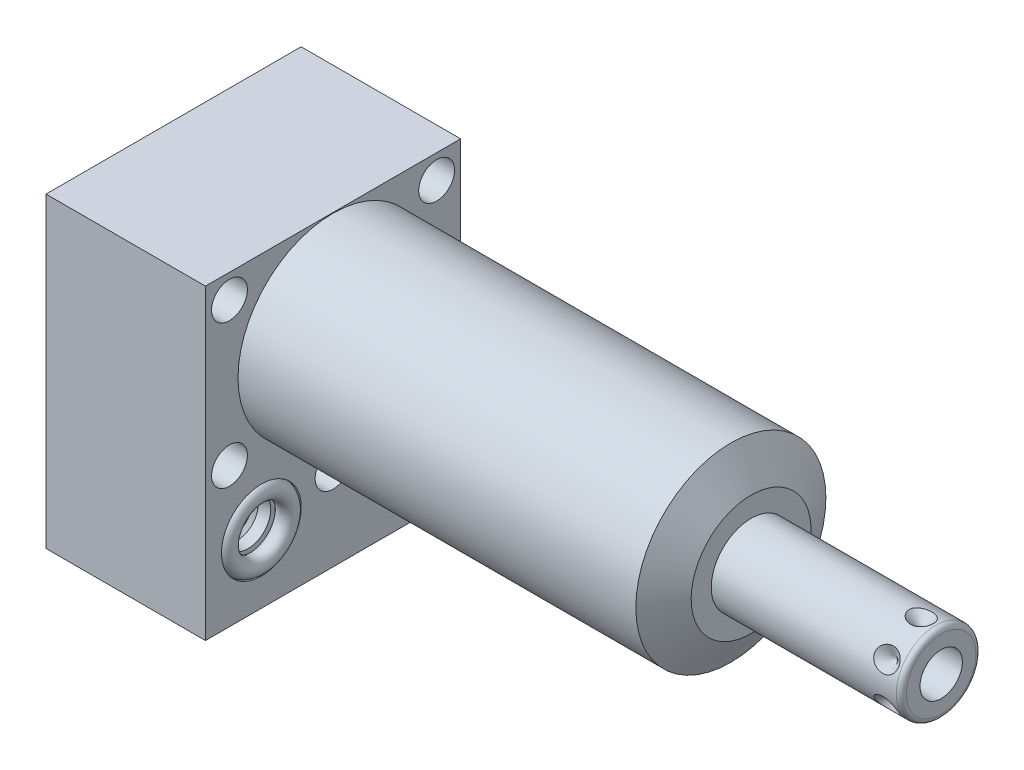
SolidWorks part; units mm, degrees
material "Alloy Steel"
ref_plane "Front Plane" through (0, 0, 0) normal (0, 0, 1) x (1, 0, 0)
ref_plane "Top Plane" through (0, 0, 0) normal (0, 1, 0) x (1, 0, 0)
ref_plane "Right Plane" through (0, 0, 0) normal (1, 0, 0) x (0, 0, -1)
ref_plane "Plane1" through (0, 0, 0) normal (1, 0, 0) x (0, 0, -1)
sketch "Sketch1" plane through (0, 0, 0) normal (1, 0, 0) x (0, 0, -1)
  line L0 (-25.4, 19.05) -> (-25.4, -42.0624)
  line L1 (-25.4, -42.0624) -> (25.4, -42.0624)
  line L2 (25.4, -42.0624) -> (25.4, 19.05)
  line L3 (25.4, 19.05) -> (-25.4, 19.05)
  line L4 (0, -47.0916) -> (0, 22.1996) construction
  dimension "D1" = 50.8
  dimension "D2" = 61.1124
  dimension "D3" = 19.05
extrude "Extrude1" add sketch "Sketch1" along normal blind 83.2358 and the other way blind 31.75
ref_plane "Plane2" through (0, 0, 0) normal (1, 0, 0) x (0, 0, -1)
sketch "Sketch2" plane through (0, 0, 0) normal (1, 0, 0) x (0, 0, -1)
  line L0 (-20.8153, 0) -> (20.8153, 0) construction
  line L6 (25.4, 19.05) -> (-25.4, 19.05)
  line L7 (-25.4, 19.05) -> (-25.4, -42.0624)
  line L8 (-25.4, -42.0624) -> (25.4, -42.0624)
  line L9 (25.4, -42.0624) -> (25.4, 19.05)
  line L10 (25.4, 19.05) -> (-25.4, 19.05)
  line L11 (-25.4, 19.05) -> (-25.4, -42.0624)
  line L12 (-25.4, -42.0624) -> (25.4, -42.0624)
  line L13 (25.4, -42.0624) -> (25.4, 19.05)
  circle A0 centre (0, 0) radius 18.923
  dimension "D1" = 37.846
  dimension "D2" = 0
extrude "Cut-Extrude1" cut sketch "Sketch2" along normal up to next
ref_plane "Plane3" through (0, 0, 0) normal (0, 0, 1) x (1, 0, 0)
sketch "Sketch3" plane through (0, 0, 0) normal (0, 0, 1) x (1, 0, 0)
  line L0 (79.203, 18.923) -> (83.2358, 11.938)
  line L1 (56.7002, 0) -> (61.1362, 0) construction
  line L2 (83.2358, 18.923) -> (83.2358, 11.938)
  line L3 (83.2358, 18.923) -> (79.203, 18.923)
  line L4 (83.2358, 18.923) -> (0, 18.923) construction
  line L5 (83.2358, -18.923) -> (83.2358, 18.923) construction
  dimension "D1" = 23.876
  dimension "D2" = 30
revolve "Cut-Revolve1" cut sketch "Sketch3" angle 360 about L1
ref_plane "Plane4" through (-29.083, -28.575, 14.2748) normal (0, 0, 1) x (0, 1, 0)
sketch "S2D0002" plane through (-29.083, -28.575, 14.2748) normal (0, 0, 1) x (0, 1, 0)
  line L0 (0, 0) -> (4.5466, 0)
  line L1 (4.5466, 0) -> (4.1066, -2.0701)
  line L2 (4.1066, -2.0701) -> (3.4544, -2.7223)
  line L3 (3.4544, -2.7223) -> (3.4544, -13.97)
  line L4 (3.4544, -13.97) -> (0, -13.97)
  line L5 (0, -13.97) -> (0, 0)
  line L6 (0, -14.6685) -> (0, 0.6985) construction
  dimension "D1" = 13.97
revolve "Cut-Revolve2" cut sketch "S2D0002" angle 360 about L6
ref_plane "Plane5" through (-29.083, -28.575, -14.2748) normal (0, 0, 1) x (0, 1, 0)
sketch "Sketch5" plane through (-29.083, -28.575, -14.2748) normal (0, 0, 1) x (0, 1, 0)
  line L0 (0, 0) -> (4.5466, 0)
  line L1 (4.5466, 0) -> (4.1066, -2.0701)
  line L2 (4.1066, -2.0701) -> (3.4544, -2.7223)
  line L3 (3.4544, -2.7223) -> (3.4544, -13.97)
  line L4 (3.4544, -13.97) -> (0, -13.97)
  line L5 (0, -13.97) -> (0, 0)
  line L6 (0, -14.6685) -> (0, 0.6985) construction
  dimension "D1" = 13.97
revolve "Cut-Revolve3" cut sketch "Sketch5" angle 360 about L6
ref_plane "Plane6" through (-2.667, -28.575, 14.2748) normal (0, 0, 1) x (0, -1, 0)
sketch "Sketch6" plane through (-2.667, -28.575, 14.2748) normal (0, 0, 1) x (0, -1, 0)
  line L0 (0, 0) -> (4.5466, 0)
  line L1 (4.5466, 0) -> (4.1066, -2.0701)
  line L2 (4.1066, -2.0701) -> (3.4544, -2.7223)
  line L3 (3.4544, -2.7223) -> (3.4544, -12.192)
  line L4 (3.4544, -12.192) -> (0, -12.192)
  line L5 (0, -12.192) -> (0, 0)
  line L6 (0, -12.8016) -> (0, 0.6096) construction
  dimension "D1" = 12.192
revolve "Cut-Revolve4" cut sketch "Sketch6" angle 360 about L6
ref_plane "Plane7" through (-2.667, -28.575, -14.2748) normal (0, 0, 1) x (0, -1, 0)
sketch "Sketch7" plane through (-2.667, -28.575, -14.2748) normal (0, 0, 1) x (0, -1, 0)
  line L0 (0, 0) -> (4.5466, 0)
  line L1 (4.5466, 0) -> (4.1066, -2.0701)
  line L2 (4.1066, -2.0701) -> (3.4544, -2.7223)
  line L3 (3.4544, -2.7223) -> (3.4544, -12.192)
  line L4 (3.4544, -12.192) -> (0, -12.192)
  line L5 (0, -12.192) -> (0, 0)
  line L6 (0, -12.8016) -> (0, 0.6096) construction
  dimension "D1" = 12.192
revolve "Cut-Revolve5" cut sketch "Sketch7" angle 360 about L6
ref_plane "Plane8" through (-15.875, -43.688, 14.2748) normal (0, 0, 1) x (-1, 0, 0)
sketch "Sketch18" plane through (-31.75, 0, 0) normal (-1, 0, 0) x (0, 0, 1)
  circle A0 centre (-14.2748, -28.575) radius 7.9375
  circle A1 centre (14.2748, -28.575) radius 7.9375
  dimension "D1" = 15.875
  dimension "D2" = 15.875
extrude "Cut-Extrude2" cut sketch "Sketch18" against normal blind 2.667
sketch "Sketch19" plane through (0, 0, 0) normal (1, 0, 0) x (0, 0, -1)
  circle A0 centre (-14.2748, -28.575) radius 7.9375
  circle A1 centre (14.2748, -28.575) radius 7.9375
  dimension "D1" = 15.875
  dimension "D2" = 15.875
extrude "Cut-Extrude3" cut sketch "Sketch19" against normal blind 2.667
sketch "Sketch8" plane through (-15.875, -43.688, 14.2748) normal (0, 0, 1) x (-1, 0, 0)
  line L0 (0, -1.8796) -> (6.1849, -1.8796)
  line L1 (6.1849, -1.8796) -> (5.6423, -4.4323)
  line L2 (5.6423, -4.4323) -> (4.9784, -5.0962)
  line L3 (4.9784, -5.0962) -> (4.9784, -20.9296)
  line L4 (4.9784, -20.9296) -> (0, -20.9296)
  line L5 (0, -20.9296) -> (0, -1.8796)
  line L6 (0, -26.67) -> (0, 1.27) construction
  line L7 (15.875, -1.6256) -> (-15.875, -1.6256) construction
  dimension "D1" = 19.05
  dimension "D2" = 0.254
revolve "Cut-Revolve6" cut sketch "Sketch8" angle 360 about L6
ref_plane "Plane9" through (-15.875, -43.688, -14.2748) normal (0, 0, 1) x (-1, 0, 0)
sketch "Sketch9" plane through (-15.875, -43.688, -14.2748) normal (0, 0, 1) x (-1, 0, 0)
  line L0 (0, -1.8796) -> (6.1849, -1.8796)
  line L1 (6.1849, -1.8796) -> (5.6423, -4.4323)
  line L2 (5.6423, -4.4323) -> (4.9784, -5.0962)
  line L3 (4.9784, -5.0962) -> (4.9784, -20.9296)
  line L4 (4.9784, -20.9296) -> (0, -20.9296)
  line L5 (0, -20.9296) -> (0, -1.8796)
  line L6 (0, -26.67) -> (0, 1.27) construction
  line L7 (15.875, -1.6256) -> (-15.875, -1.6256) construction
  dimension "D1" = 19.05
  dimension "D2" = 0.254
revolve "Cut-Revolve7" cut sketch "Sketch9" angle 360 about L6
ref_plane "Plane10" through (0, 0, 0) normal (0, 0, 1) x (1, 0, 0)
sketch "Sketch20" plane through (0, -42.0624, 0) normal (0, -1, 0) x (1, 0, 0)
  circle A0 centre (-15.875, 14.2748) radius 9.525
  circle A1 centre (-15.875, -14.2748) radius 9.525
  dimension "D1" = 19.05
extrude "Cut-Extrude4" cut sketch "Sketch20" against normal blind 0.254
sketch "Sketch10" plane through (0, 0, 0) normal (0, 0, 1) x (1, 0, 0)
  line L0 (83.2358, 0) -> (83.2358, 7.9375)
  line L1 (83.2358, 7.9375) -> (120.0658, 7.9375)
  line L2 (121.0818, 6.9215) -> (121.0818, 0)
  line L3 (121.0818, 0) -> (83.2358, 0)
  line L4 (59.5935, 0) -> (89.0981, 0) construction
  line L5 (83.2358, -11.938) -> (83.2358, 11.938) construction
  line L6 (-31.75, 19.05) -> (-31.75, -42.0624) construction
  arc A0 (121.0818, 6.9215) -> (120.0658, 7.9375) centre (120.0658, 6.9215) ccw
  point P0 (60.9346, 0)
  dimension "D2" = 1.016
  dimension "D1" = 15.875
  dimension "D3" = 152.8318
revolve "Revolve1" add sketch "Sketch10" angle 360 about L4
ref_plane "Plane11" through (87.757, -4.2164, 0) normal (0, 0, 1) x (0, -1, 0)
sketch "S2D0001" plane through (87.757, -4.2164, 0) normal (0, 0, 1) x (0, -1, 0)
  line L0 (0, 33.3248) -> (0, 18.0848)
  line L1 (0, 18.0848) -> (-4.2164, 15.5513)
  line L2 (0, 33.3248) -> (-4.2164, 33.3248)
  line L3 (-4.2164, 33.3248) -> (-4.2164, 15.5513)
  line L4 (-4.2164, -24.865) -> (-4.2164, 0.8887) construction
  line L5 (2.7051, 33.3248) -> (-11.1379, 33.3248) construction
  dimension "D1" = 8.4328
  dimension "D2" = 59
  dimension "D3" = 15.24
revolve "Cut-Revolve8" cut sketch "S2D0001" angle 360 about L4
ref_plane "Plane14" through (0, -28.575, -14.2748) normal (0, -1, 0) x (0, 0, -1)
sketch "Sketch14" plane through (0, -28.575, -14.2748) normal (0, -1, 0) x (0, 0, -1)
  line L0 (0, -2.8435) -> (0, 1.0401) construction
  line L1 (0, -2.667) -> (0, -4.7371) construction
  line L2 (7.9375, -2.667) -> (-7.9375, -2.667) construction
  circle A0 centre (6.1722, -0.9017) radius 1.7653
  dimension "D1" = 3.5306
  dimension "D2" = 12.3444
revolve "Revolve2" add sketch "Sketch14" angle 360 about L0
ref_plane "Plane15" through (0, -28.575, -14.2748) normal (0, -1, 0) x (0, 0, -1)
sketch "Sketch15" plane through (0, -28.575, -14.2748) normal (0, -1, 0) x (0, 0, -1)
  line L0 (0, -32.7901) -> (0, -28.9065) construction
  line L1 (0, -26.3607) -> (0, -19.4599) construction
  line L2 (-7.9375, -29.083) -> (7.9375, -29.083) construction
  circle A0 centre (6.1722, -30.8483) radius 1.7653
  dimension "D1" = 3.5306
  dimension "D2" = 12.3444
revolve "Revolve3" add sketch "Sketch15" angle 360 about L0
ref_plane "Plane16" through (83.7946, -7.9375, 0) normal (0, 0, 1) x (-1, 0, 0)
sketch "Sketch16" plane through (83.7946, -7.9375, 0) normal (0, 0, 1) x (-1, 0, 0)
  line L0 (-33.3248, 0) -> (-30.9118, 0)
  line L1 (-30.9118, 0) -> (-33.3248, -2.413)
  line L2 (-33.3248, 0) -> (-33.3248, -2.413)
  line L3 (-33.3248, -3.8054) -> (-33.3248, 0.1207) construction
  line L4 (0.5588, 0) -> (-36.2712, 0) construction
  line L5 (-37.2872, -1.016) -> (-37.2872, -14.859) construction
  dimension "D1" = 3.9624
  dimension "D2" = 4.826
  dimension "D3" = 45
revolve "Cut-Revolve9" cut sketch "Sketch16" angle 360 about L3
pattern_circular "CirPattern1" count 6 over 360 about axis through (83.2368, 0, 0) along (-1, 0, 0) of "Cut-Revolve9"
hole_wizard "Hole1" positions "Sketch22" profile "Sketch21" legacy end condition up to next
sketch "Sketch22" plane through (0, 0, 0) normal (1, 0, 0) x (0, 0, -1)
  line L0 (0, 0) -> (-32.1908, 0) construction
  point P0 (-20.6248, 14.2748)
  point P1 (0, -25.0952)
  point P13 (-20.6248, -14.2748)
  point P14 (20.6248, 14.2748)
  point P15 (20.6248, -14.2748)
  dimension "D2" = 14.2748
  dimension "D3" = 25.0952
sketch "Sketch21" plane through (0, 14.2748, 20.6248) normal (0, 1, 0) x (0, 0, -1)
  line L0 (0, 0) -> (0, 31.75)
  line L1 (0, 31.75) -> (3.5687, 31.75)
  line L2 (3.5687, 31.75) -> (3.5687, 0)
  line L3 (3.5687, 0) -> (0, 0)
  line L4 (0, 110) -> (0, -10) construction
  dimension "Diameter" = 7.1374
  dimension "Depth" = 31.75
pattern_linear "LPattern1" count 2 spacing 28.5496 along (0, 0, 1) of "Revolve3", "Revolve2"
